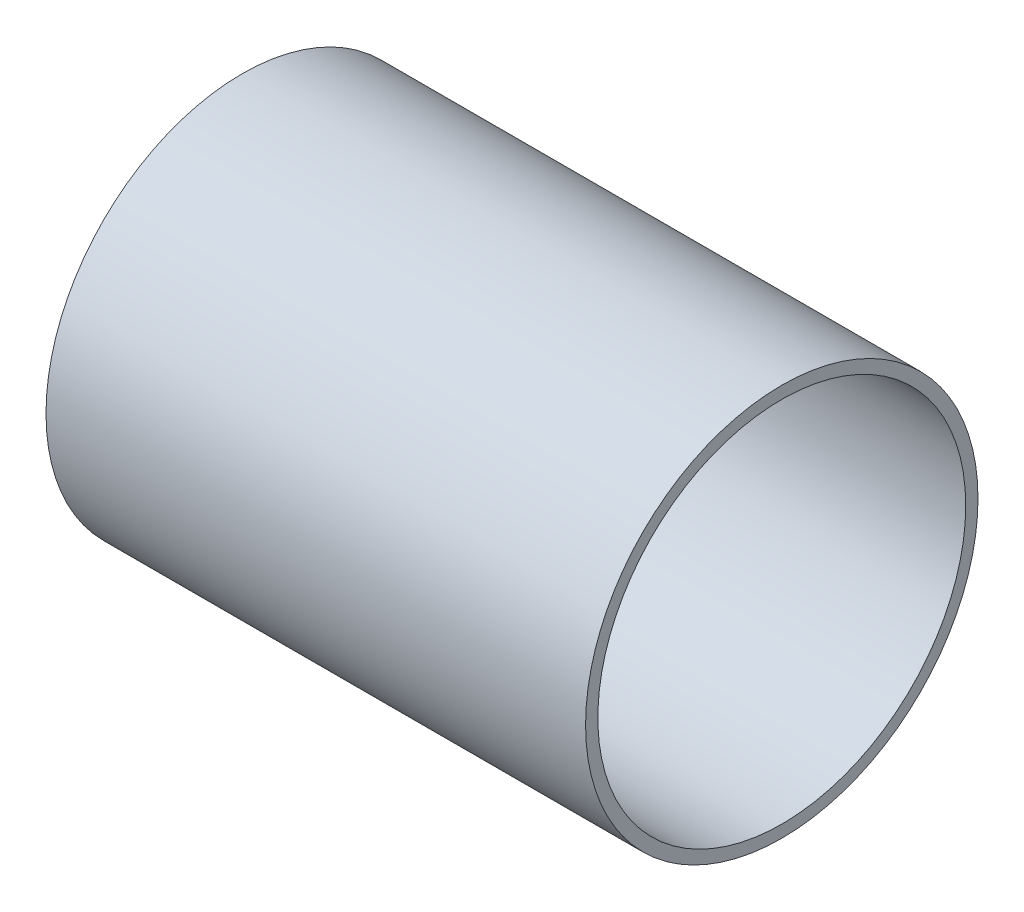
SolidWorks part; units mm, degrees
material "PC High Viscosity"
ref_plane "Front" through (0, 0, 0) normal (0, 0, 1) x (1, 0, 0)
ref_plane "Top" through (0, 0, 0) normal (0, 1, 0) x (1, 0, 0)
ref_plane "Right" through (0, 0, 0) normal (1, 0, 0) x (0, 0, -1)
other "Appearance"
sketch "Sketch1" plane through (0, 0, 0) normal (1, 0, 0) x (0, 0, -1)
  circle A0 centre (0, 0) radius 50.8
  circle A1 centre (0, 0) radius 47.625
  dimension "D1" = 101.6
  dimension "D2" = 95.25
extrude "Boss-Extrude1" add sketch "Sketch1" along normal blind 139.7
equation "\"D2@Sketch1\"=\"D1@Sketch1\"-.25"
